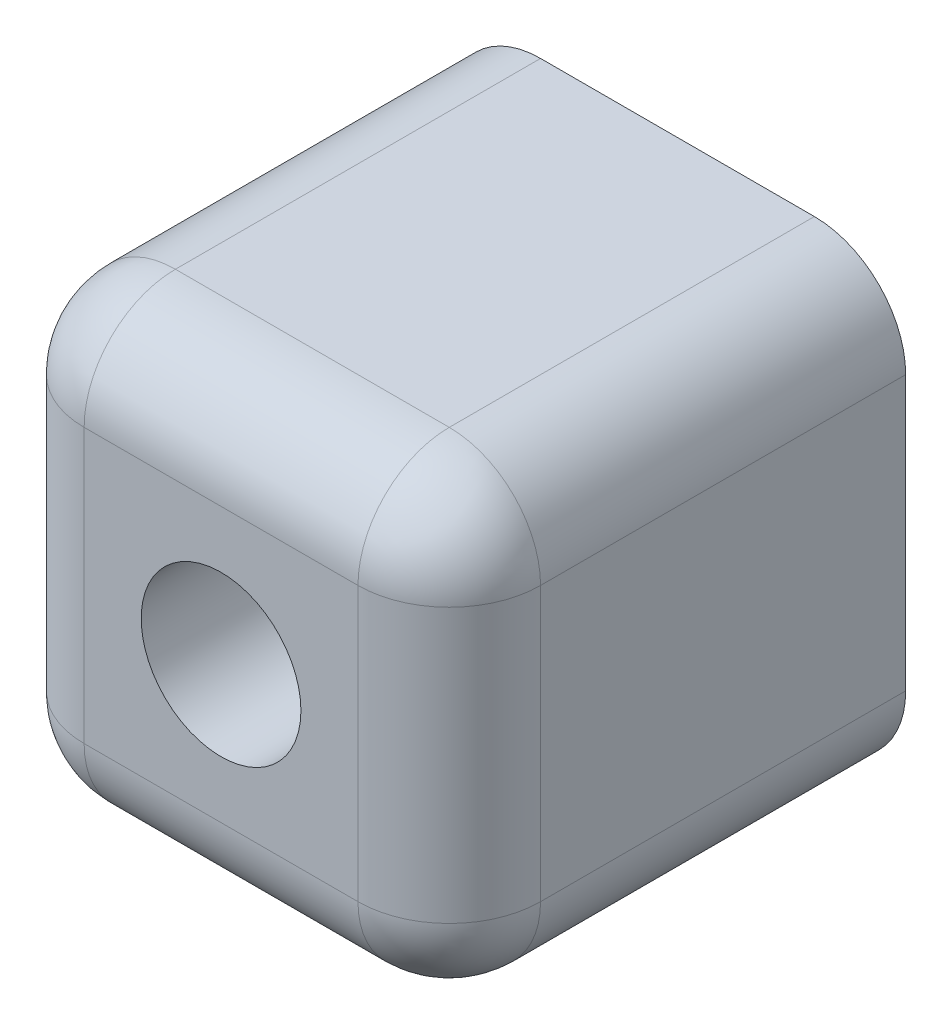
SolidWorks part; units mm, degrees
ref_plane "Front Plane" through (0, 0, 0) normal (0, 0, 1) x (1, 0, 0)
ref_plane "Top Plane" through (0, 0, 0) normal (0, 1, 0) x (1, 0, 0)
ref_plane "Right Plane" through (0, 0, 0) normal (1, 0, 0) x (0, 0, -1)
sketch "Sketch1" plane through (0, 0, 0) normal (0, 0, 1) x (1, 0, 0)
  line L1 (0, 0) -> (10, 0)
  line L2 (0, 0) -> (0, 10)
  line L3 (0, 10) -> (10, 10)
  line L4 (10, 0) -> (10, 10)
  dimension "D1" = 10
  dimension "D2" = 10
extrude "Boss-Extrude1" add sketch "Sketch1" along normal blind 10
sketch "Sketch2" plane through (0, 0, 10) normal (0, 0, 1) x (1, 0, 0)
  line L0 (0, 0) -> (10, 0) construction
  line L1 (0, 10) -> (0, 0) construction
  circle A0 centre (5, 5) radius 1.75
  dimension "D3" = 3.5
  dimension "D1" = 5
  dimension "D2" = 5
extrude "Cut-Extrude1" cut sketch "Sketch2" against normal through all
sketch "Sketch3" plane through (0, 0, 0) normal (0, 0, -1) x (-1, 0, 0)
  circle A0 centre (-5, 5) radius 2.05
  dimension "D1" = 4.1
extrude "Cut-Extrude2" cut sketch "Sketch3" against normal blind 5
fillet "Fillet1" radius 2 4 edges at (10, 10, 5) (0, 10, 5) (0, 0, 5) (10, 0, 5)
fillet "Fillet2" radius 2 8 edges at (0.5858, 0.5858, 10) (0, 5, 10) (0.5858, 9.4142, 10) (5, 10, 10) (9.4142, 9.4142, 10) (10, 5, 10) (9.4142, 0.5858, 10) (5, 0, 10)
